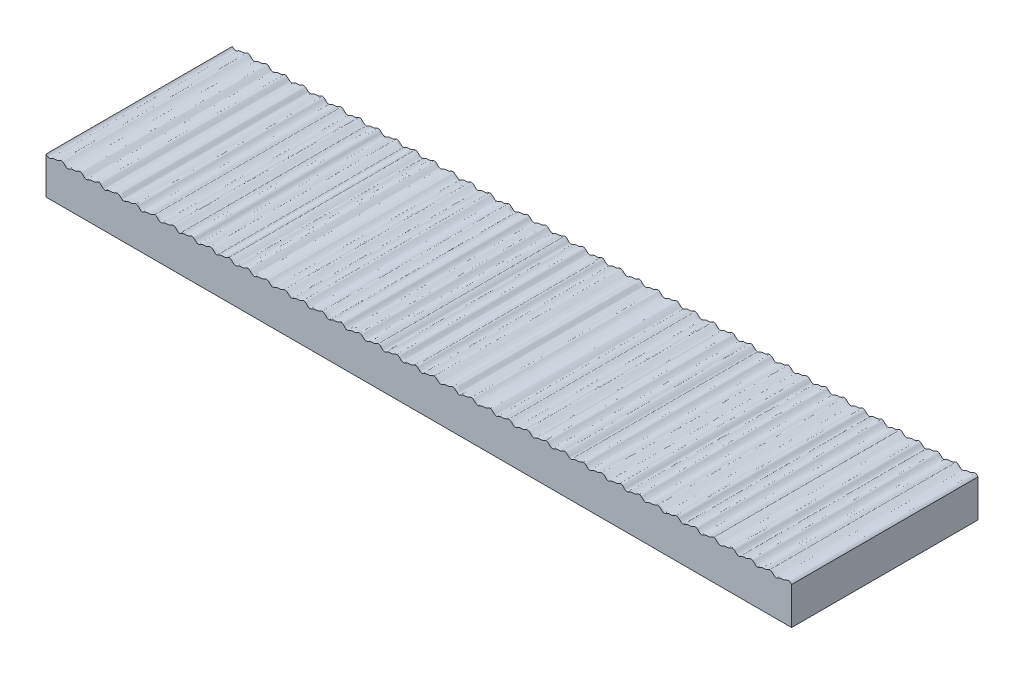
SolidWorks part; units mm, degrees
ref_plane "Ebene vorne" through (0, 0, 0) normal (0, 0, 1) x (1, 0, 0)
ref_plane "Ebene oben" through (0, 0, 0) normal (0, 1, 0) x (1, 0, 0)
ref_plane "Ebene rechts" through (0, 0, 0) normal (1, 0, 0) x (0, 0, -1)
sketch "Skizze1" plane through (0, 0, 0) normal (0, 0, 1) x (1, 0, 0)
  line L0 (0, 10) -> (200, 10) construction
  line L1 (0, 10) -> (0, 0)
  line L2 (0, 0) -> (200, 0)
  line L3 (200, 0) -> (200, 10)
  line L4 (0, 9.5017) -> (200, 9.5017) construction
  line L5 (4.9999, 10) -> (4.9999, 0) construction
  spline S0 degree 4 poles (-19.8, 9.8128) (-19.7132, 9.727) (-19.5652, 9.6108) (-19.3313, 9.4839) (-19.0053, 9.5005) (-18.756, 9.6033) (-18.5037, 9.7471) (-18.2268, 9.8968) (-17.899, 9.9991) (-17.5329, 10.0025) (-17.1781, 9.9937) (-16.8421, 10.0743) (-16.5441, 10.2237) (-16.269, 10.3856) (-15.9702, 10.5157) (-15.6449, 10.5039) (-15.3665, 10.3418) (-15.1366, 10.1344) (-14.8874, 9.8911) (-14.613, 9.6251) (-14.2253, 9.4318) (-13.8044, 9.5667) (-13.4774, 9.7665) (-13.1471, 9.9336) (-12.7787, 10.0119) (-12.3948, 9.9918) (-12.003, 10.014) (-11.6283, 10.1713) (-11.2949, 10.3742) (-10.9166, 10.5481) (-10.5226, 10.4647) (-10.2351, 10.2274) (-9.9864, 9.9872) (-9.7489, 9.7562) (-9.4941, 9.5595) (-9.1984, 9.4737) (-8.9158, 9.5299) (-8.6755, 9.6479) (-8.4177, 9.7964) (-8.1186, 9.9433) (-7.7567, 10.0153) (-7.3586, 9.9875) (-6.9251, 10.0301) (-6.5623, 10.2086) (-6.2539, 10.4005) (-5.9205, 10.5185) (-5.6177, 10.4936) (-5.3452, 10.326) (-5.1071, 10.1058) (-4.8595, 9.8627) (-4.5902, 9.6128) (-4.2208, 9.4424) (-3.8205, 9.5583) (-3.4963, 9.7556) (-3.1609, 9.929) (-2.7804, 10.0137) (-2.3814, 9.9896) (-1.9713, 10.0188) (-1.5811, 10.1958) (-1.257, 10.4006) (-0.9071, 10.5319) (-0.5771, 10.4741) (-0.3263, 10.3084) (-0.0768, 10.0763) (0.056, 9.9441) (0.2767, 9.7371) (0.4956, 9.5743) (0.7544, 9.48) (1.05, 9.5113) (1.3273, 9.6477) (1.6012, 9.8088) (1.9021, 9.9471) (2.2375, 10.009) (2.5868, 9.994) (2.9465, 10.0097) (3.2633, 10.1208) (3.531, 10.269) (3.7764, 10.4067) (4.0174, 10.5009) (4.2937, 10.5121) (4.5645, 10.3933) (4.8005, 10.1959) (5.0283, 9.9711) (5.2688, 9.7419) (5.5521, 9.5241) (5.9206, 9.4608) (6.2669, 9.6123) (6.5703, 9.7924) (6.8913, 9.9463) (7.2504, 10.0115) (7.6239, 9.991) (8.0086, 10.018) (8.3767, 10.1744) (8.6908, 10.3651) (9.0184, 10.5173) (9.3632, 10.5017) (9.6434, 10.3346) (9.8801, 10.1192) (10.1091, 9.8914) (10.3449, 9.6751) (10.622, 9.5036) (10.9686, 9.4786) (11.3025, 9.6302) (11.6207, 9.8248) (11.9967, 9.9846) (12.3936, 10.0089) (12.7833, 9.9873) (13.161, 10.0708) (13.4966, 10.2452) (13.8028, 10.4296) (14.1427, 10.5368) (14.4726, 10.4522) (14.7294, 10.2603) (14.9582, 10.0419) (15.1851, 9.8181) (15.4295, 9.6095) (15.7306, 9.4725) (16.0842, 9.5156) (16.41, 9.6969) (16.7477, 9.8935) (17.1559, 10.0141) (17.5531, 9.9934) (17.9271, 10.0064) (18.2618, 10.12) (18.5491, 10.2781) (18.8425, 10.4467) (19.1956, 10.5461) (19.539, 10.4192) (19.8022, 10.1924) (20.0371, 9.9636) (20.2623, 9.7466) (20.5116, 9.558) (20.8082, 9.4716) (21.1028, 9.5343) (21.3593, 9.6673) (21.617, 9.8163) (21.9007, 9.9454) (22.2191, 10.0064) (22.5538, 9.9968) (22.8831, 10.0033) (23.1957, 10.0912) (23.4781, 10.2368) (23.7453, 10.3932) (24.0343, 10.5142) (24.3441, 10.5037) (24.611, 10.3572) (24.8317, 10.1652) (25.0712, 9.9305) (25.3361, 9.6732) (25.687, 9.4499) (26.0987, 9.5211) (26.4123, 9.6997) (26.6971, 9.8597) (27.0176, 9.9809) (27.371, 10.0095) (27.7381, 9.987) (28.1136, 10.0531) (28.4763, 10.228) (28.8222, 10.4523) (29.2422, 10.5605) (29.6076, 10.3674) (29.8689, 10.1296) (30.0989, 9.9014) (30.3447, 9.6748) (30.6533, 9.4801) (31.0349, 9.4907) (31.3718, 9.6755) (31.6945, 9.8617) (32.0528, 9.9935) (32.4275, 10.0052) (32.7994, 9.9904) (33.1624, 10.0725) (33.4892, 10.2413) (33.7899, 10.4213) (34.1235, 10.5353) (34.4555, 10.4619) (34.7162, 10.2721) (34.9451, 10.0549) (35.1703, 9.8324) (35.4119, 9.6227) (35.7099, 9.4756) (36.0694, 9.5082) (36.4027, 9.6921) (36.7453, 9.8933) (37.1618, 10.016) (37.5686, 9.9916) (37.955, 10.01) (38.3008, 10.1379) (38.5986, 10.3073) (38.8972, 10.4735) (39.2404, 10.5347) (39.5538, 10.4026) (39.7994, 10.1958) (40.0243, 9.9758) (40.2479, 9.7603) (40.5015, 9.5621) (40.8224, 9.4624) (41.1625, 9.5539) (41.4684, 9.7328) (41.7894, 9.9084) (42.1555, 10.0071) (42.5227, 9.9977) (42.8799, 10.0002) (43.2154, 10.0978) (43.5138, 10.257) (43.8102, 10.4307) (44.163, 10.5466) (44.5145, 10.4359) (44.7827, 10.2106) (45.0196, 9.9811) (45.2463, 9.7608) (45.4921, 9.5695) (45.7813, 9.4746) (46.0693, 9.5229) (46.3189, 9.6442) (46.5707, 9.7902) (46.8484, 9.927) (47.1677, 10.0039) (47.5116, 9.9992) (47.8484, 9.9984) (48.169, 10.0798) (48.4573, 10.2246) (48.7268, 10.3831) (49.0125, 10.5086) (49.3176, 10.5095) (49.5819, 10.3772) (49.7978, 10.197) (50.0353, 9.9657) (50.2999, 9.707) (50.6415, 9.4588) (51.0649, 9.5058) (51.3834, 9.6827) (51.6631, 9.8419) (51.976, 9.9702) (52.3236, 10.0107) (52.6857, 9.9883) (53.0576, 10.0353) (53.4288, 10.1996) (53.7766, 10.4255) (54.1972, 10.5686) (54.5817, 10.3889) (54.8482, 10.1492) (55.078, 9.922) (55.3219, 9.6944) (55.6232, 9.4909) (56.0024, 9.48) (56.3413, 9.6571) (56.6566, 9.841) (57.0019, 9.9812) (57.3723, 10.009) (57.7455, 9.9879) (58.1184, 10.0542) (58.4601, 10.2234) (58.7656, 10.4087) (59.0994, 10.5327) (59.4345, 10.4719) (59.6985, 10.2877) (59.9288, 10.0711) (60.1551, 9.8468) (60.395, 9.6354) (60.687, 9.4819) (61.0423, 9.499) (61.374, 9.6742) (61.7071, 9.873) (62.1099, 10.0089) (62.5069, 9.9977) (62.8809, 9.9991) (63.2202, 10.1008) (63.5114, 10.2558) (63.8032, 10.426) (64.1495, 10.5453) (64.5013, 10.4441) (64.7713, 10.2213) (65.0069, 9.9933) (65.2327, 9.7751) (65.5033, 9.5547) (65.884, 9.4445) (66.2644, 9.6064) (66.5993, 9.8128) (66.9589, 9.9696) (67.3267, 10.0107) (67.6846, 9.9895) (68.0293, 10.0315) (68.3405, 10.1598) (68.6192, 10.3197) (68.9196, 10.483) (69.2883, 10.5375) (69.636, 10.3531) (69.9168, 10.0783) (70.2112, 9.7989) (70.5572, 9.4869) (71.0322, 9.466) (71.4097, 9.7065) (71.761, 9.8916) (72.1231, 10.0046) (72.4974, 9.9999) (72.8717, 9.9957) (73.2335, 10.1028) (73.5597, 10.2828) (73.8856, 10.4755) (74.2818, 10.5433) (74.6402, 10.3492) (74.9206, 10.0747) (75.2149, 9.7951) (75.5626, 9.484) (76.0379, 9.4683) (76.4142, 9.7094) (76.7662, 9.8939) (77.1285, 10.0053) (77.5027, 9.9995) (77.877, 9.9963) (78.2383, 10.105) (78.564, 10.2854) (78.8905, 10.4779) (79.2872, 10.5422) (79.6441, 10.3457) (79.9244, 10.0709) (80.2185, 9.7918) (80.5681, 9.4804) (81.0528, 9.4717) (81.4399, 9.7258) (81.8166, 9.9208) (82.2185, 10.0176) (82.6095, 9.9889) (82.983, 10.0173) (83.3181, 10.147) (83.611, 10.3148) (83.9215, 10.4861) (84.3006, 10.537) (84.6481, 10.3407) (84.9279, 10.0713) (85.1793, 9.8221) (85.426, 9.6138) (85.6898, 9.4972) (85.9409, 9.4912) (86.2167, 9.5855) (86.4994, 9.7497) (86.8216, 9.9268) (87.2241, 10.0156) (87.6148, 9.9895) (87.9883, 10.0181) (88.3227, 10.1495) (88.6153, 10.3174) (88.9265, 10.4882) (89.306, 10.5358) (89.6521, 10.3372) (89.9317, 10.0677) (90.1831, 9.8183) (90.4306, 9.6106) (90.6953, 9.4959) (90.9465, 9.4923) (91.2217, 9.5882) (91.5041, 9.7525) (91.8268, 9.9289) (92.2295, 10.0158) (92.6201, 9.9892) (92.9935, 10.0194) (93.3273, 10.1519) (93.6197, 10.32) (93.9314, 10.4902) (94.3114, 10.5345) (94.6561, 10.3336) (94.9354, 10.064) (95.187, 9.8146) (95.4352, 9.6074) (95.7009, 9.4947) (95.9521, 9.4934) (96.2266, 9.5908) (96.5088, 9.7554) (96.832, 9.9311) (97.235, 10.0159) (97.6255, 9.9888) (97.9986, 10.0207) (98.3321, 10.1542) (98.6236, 10.3231) (98.9056, 10.474) (99.2035, 10.5241) (99.4679, 10.4432) (99.6773, 10.3016) (99.8669, 10.1308) (100.0515, 9.949) (100.2431, 9.7658) (100.4584, 9.5966) (100.7245, 9.4824) (101.0266, 9.5028) (101.3082, 9.6369) (101.5812, 9.7975) (101.8792, 9.9391) (102.2124, 10.0078) (102.5609, 9.9957) (102.9197, 10.0051) (103.239, 10.1094) (103.5091, 10.2561) (103.7553, 10.3959) (103.9971, 10.496) (104.2846, 10.5168) (104.5754, 10.3903) (104.8277, 10.1705) (105.0802, 9.92) (105.3443, 9.6707) (105.6839, 9.4635) (106.0872, 9.5085) (106.4264, 9.7098) (106.7634, 9.8963) (107.1347, 10.0069) (107.5036, 9.9984) (107.8569, 9.9988) (108.1849, 10.0861) (108.4725, 10.2335) (108.76, 10.4011) (109.0962, 10.54) (109.4592, 10.4711) (109.7431, 10.2478) (109.9854, 10.0146) (110.2184, 9.7885) (110.4952, 9.5571) (110.8906, 9.4405) (111.2824, 9.6165) (111.6276, 9.8298) (112.0062, 9.9843) (112.3877, 10.0085) (112.7533, 9.9888) (113.0968, 10.0528) (113.3973, 10.1911) (113.6655, 10.3463) (113.9602, 10.4965) (114.3164, 10.5274) (114.6237, 10.3528) (114.8676, 10.1305) (115.0879, 9.9127) (115.2996, 9.7167) (115.5651, 9.5259) (115.9297, 9.4576) (116.3055, 9.6298) (116.6653, 9.853) (117.0908, 10.0124) (117.5404, 9.9944) (117.9485, 10.0031) (118.2912, 10.1356) (118.5689, 10.2905) (118.8107, 10.4241) (119.1178, 10.5331) (119.4895, 10.4658) (119.768, 10.2241) (120.0149, 9.9854) (120.2325, 9.7764) (120.4317, 9.6173) (120.7176, 9.4735) (121.1079, 9.5064) (121.4527, 9.7323) (121.8387, 9.9324) (122.2456, 10.0143) (122.6276, 9.9896) (122.9863, 10.0184) (123.3001, 10.1402) (123.5697, 10.2909) (123.8194, 10.4299) (124.0953, 10.5212) (124.3827, 10.4871) (124.6302, 10.3409) (124.8407, 10.156) (125.0716, 9.9299) (125.3295, 9.6814) (125.6694, 9.4565) (126.0839, 9.5126) (126.4045, 9.6952) (126.6992, 9.8617) (127.03, 9.9848) (127.3919, 10.0088) (127.7645, 9.9868) (128.1421, 10.063) (128.4972, 10.2422) (128.8378, 10.4578) (129.2536, 10.5565) (129.6239, 10.3586) (129.8954, 10.1026) (130.1526, 9.8512) (130.4387, 9.5879) (130.858, 9.4277) (131.2756, 9.61) (131.6255, 9.8302) (132.0056, 9.9826) (132.3786, 10.0086) (132.7414, 9.9891) (133.0874, 10.0485) (133.3951, 10.1892) (133.6732, 10.3519) (133.9828, 10.5071) (134.3571, 10.5201) (134.6871, 10.305) (134.9654, 10.0346) (135.2178, 9.7846) (135.4728, 9.5825) (135.7455, 9.4865) (135.9966, 9.5036) (136.2663, 9.6125) (136.5465, 9.7779) (136.8742, 9.9476) (137.2786, 10.0158) (137.6682, 9.9867) (138.0401, 10.0317) (138.3686, 10.1739) (138.6587, 10.3435) (138.9766, 10.5074) (139.3591, 10.5206) (139.691, 10.3013) (139.9692, 10.031) (140.2217, 9.7808) (140.4776, 9.5795) (140.7512, 9.4857) (141.0022, 9.5051) (141.2712, 9.6153) (141.5513, 9.7807) (141.8795, 9.9496) (142.2841, 10.0157) (142.6736, 9.9865) (143.0452, 10.0332) (143.3732, 10.1764) (143.6631, 10.3461) (143.9817, 10.5092) (144.3643, 10.5188) (144.6948, 10.2977) (144.9729, 10.0273) (145.2255, 9.7771) (145.4824, 9.5765) (145.7568, 9.485) (146.0077, 9.5066) (146.2762, 9.618) (146.5561, 9.7835) (146.8849, 9.9515) (147.2896, 10.0156) (147.679, 9.9864) (148.0503, 10.0347) (148.3778, 10.1788) (148.6673, 10.3489) (148.9827, 10.5084) (149.3547, 10.518) (149.6765, 10.3125) (149.9446, 10.0556) (150.1902, 9.8116) (150.4391, 9.6041) (150.7153, 9.4881) (150.9866, 9.4982) (151.2695, 9.6128) (151.5567, 9.7845) (151.8902, 9.9533) (152.295, 10.0154) (152.6843, 9.9862) (153.0555, 10.0362) (153.3823, 10.1813) (153.6717, 10.3515) (153.9878, 10.5101) (154.3599, 10.5162) (154.6804, 10.309) (154.9483, 10.0519) (155.194, 9.8079) (155.4437, 9.6009) (155.7209, 9.487) (155.9921, 9.4997) (156.2745, 9.6156) (156.5615, 9.7873) (156.8956, 9.9552) (157.3005, 10.0153) (157.6897, 9.9861) (158.0606, 10.0378) (158.3868, 10.1838) (158.6761, 10.3541) (158.9929, 10.5117) (159.3651, 10.5144) (159.6842, 10.3055) (159.952, 10.0482) (160.1979, 9.8042) (160.4484, 9.5978) (160.7265, 9.486) (160.9977, 9.5012) (161.2794, 9.6184) (161.5662, 9.7901) (161.901, 9.9571) (162.306, 10.0151) (162.6951, 9.9859) (163.0657, 10.0394) (163.3914, 10.1863) (163.6804, 10.3567) (163.998, 10.5133) (164.3702, 10.5126) (164.6881, 10.3019) (164.9558, 10.0445) (165.2017, 9.8005) (165.453, 9.5946) (165.7321, 9.485) (166.0032, 9.5027) (166.2843, 9.6213) (166.571, 9.7929) (166.9064, 9.9589) (167.3114, 10.0148) (167.7004, 9.9858) (168.0708, 10.041) (168.3959, 10.1888) (168.6848, 10.3593) (169.0032, 10.5149) (169.3753, 10.5107) (169.6919, 10.2984) (169.9595, 10.0409) (170.2056, 9.7967) (170.4577, 9.5915) (170.7377, 9.4841) (171.0088, 9.5043) (171.2932, 9.6258) (171.5862, 9.8021) (171.9356, 9.9711) (172.3588, 10.0139) (172.7563, 9.9844) (173.1239, 10.06) (173.4361, 10.2123) (173.7115, 10.3743) (174.0212, 10.5173) (174.3841, 10.5062) (174.6957, 10.2949) (174.9632, 10.0372) (175.2094, 9.793) (175.4624, 9.5884) (175.7434, 9.4832) (176.0143, 9.5059) (176.2981, 9.6286) (176.591, 9.8049) (176.941, 9.9728) (177.3642, 10.0135) (177.7617, 9.9845) (178.1289, 10.0619) (178.4406, 10.2148) (178.7159, 10.3769) (179.0222, 10.5164) (179.3746, 10.5061) (179.6774, 10.3095) (179.9347, 10.0656) (180.174, 9.8275) (180.4198, 9.6172) (180.7016, 9.487) (180.993, 9.4969) (181.2955, 9.626) (181.6018, 9.8122) (181.9706, 9.9844) (182.4114, 10.0105) (182.8177, 9.9856) (183.1809, 10.0833) (183.4807, 10.2386) (183.743, 10.3904) (184.0404, 10.5183) (184.3833, 10.5017) (184.6813, 10.3061) (184.9385, 10.0619) (185.1778, 9.8238) (185.4243, 9.6139) (185.7072, 9.4858) (185.9985, 9.4984) (186.3003, 9.6289) (186.6066, 9.815) (186.9761, 9.9859) (187.4168, 10.0099) (187.8231, 9.986) (188.1858, 10.0853) (188.4852, 10.2412) (188.7474, 10.3929) (189.0456, 10.5195) (189.3883, 10.4997) (189.6852, 10.3027) (189.9422, 10.0582) (190.1816, 9.8201) (190.4289, 9.6106) (190.7128, 9.4846) (191.0041, 9.5) (191.3052, 9.6318) (191.6114, 9.8177) (191.9816, 9.9874) (192.4222, 10.0092) (192.8285, 9.9864) (193.1907, 10.0874) (193.4896, 10.2438) (193.7519, 10.3954) (194.0508, 10.5207) (194.3934, 10.4977) (194.6891, 10.2992) (194.9459, 10.0545) (195.1854, 9.8164) (195.4335, 9.6074) (195.7184, 9.4835) (196.0097, 9.5016) (196.3101, 9.6347) (196.6162, 9.8205) (196.9872, 9.9888) (197.4276, 10.0086) (197.8339, 9.9869) (198.1953, 10.0897) (198.4955, 10.2454) (198.7505, 10.4022) (199.1, 10.5235) (199.4629, 10.5031) (199.8859, 10.1151) (200.0712, 9.9273) (200.4553, 9.569) (200.8296, 9.4493) (201.2486, 9.5872) (201.5887, 9.8119) (201.9923, 9.9888) (202.4296, 10.0087) (202.8367, 9.987) (203.1973, 10.0904) (203.4955, 10.2472) (203.7576, 10.3985) (204.057, 10.5219) (204.399, 10.4953) (204.6931, 10.2955) (204.9496, 10.0508) (205.189, 9.8129) (205.4375, 9.6046) (205.7231, 9.4827) (206.014, 9.5029) (206.3136, 9.6368) (206.6195, 9.8223) (206.9906, 9.9896) (207.4305, 10.0082) (207.8363, 9.9872) (208.1974, 10.0903) (208.4955, 10.2472) (208.7576, 10.3985) (209.057, 10.5219) (209.399, 10.4953) (209.6931, 10.2955) (209.9496, 10.0508) (210.189, 9.8129) (210.4375, 9.6046) (210.7231, 9.4827) (211.014, 9.5029) (211.3136, 9.6368) (211.6195, 9.8223) (211.9906, 9.9896) (212.4305, 10.0082) (212.8363, 9.9872) (213.1974, 10.0903) (213.4955, 10.2472) (213.7576, 10.3985) (214.057, 10.5219) (214.399, 10.4953) (214.6931, 10.2955) (214.9496, 10.0508) (215.189, 9.8129) (215.4375, 9.6046) (215.7231, 9.4827) (216.014, 9.5029) (216.3123, 9.6363) (216.6162, 9.8202) (216.983, 9.9866) (217.4171, 10.0097) (217.8329, 9.9851) (218.2196, 10.096) (218.5508, 10.2782) (218.8619, 10.4609) (219.2613, 10.5498) (219.5473, 10.4039) (219.7135, 10.273) (219.7999, 10.1873) knots 0 0 0 0 0 0.001825 0.002828 0.003831 0.004834 0.005837 0.007212 0.008586 0.009961 0.011336 0.012548 0.013761 0.014973 0.016185 0.017355 0.018526 0.019697 0.020867 0.022616 0.024365 0.025745 0.027126 0.028507 0.029888 0.031392 0.032896 0.0344 0.035904 0.037402 0.0389 0.040156 0.041413 0.042669 0.043926 0.044928 0.04593 0.046932 0.047934 0.049435 0.050935 0.052436 0.053937 0.055942 0.056945 0.057948 0.059177 0.060406 0.061634 0.062863 0.064424 0.065985 0.067399 0.068812 0.070226 0.07164 0.073225 0.07481 0.076395 0.077981 0.079102 0.080224 0.081345 0.082467 0.083446 0.084425 0.085404 0.086382 0.087588 0.088794 0.09 0.091205 0.092557 0.093908 0.095259 0.096611 0.097574 0.098537 0.0995 0.100463 0.101676 0.102889 0.104101 0.105314 0.106733 0.108153 0.109481 0.11081 0.112139 0.113468 0.114953 0.116437 0.117921 0.119406 0.120574 0.121743 0.122967 0.124191 0.125415 0.126639 0.12781 0.12898 0.130495 0.132009 0.133523 0.135038 0.136457 0.137876 0.139295 0.140715 0.141888 0.14306 0.144268 0.145476 0.146684 0.147892 0.149098 0.150303 0.151879 0.153455 0.155031 0.156607 0.157844 0.159081 0.160318 0.161555 0.162973 0.164392 0.165578 0.166763 0.167949 0.169135 0.170218 0.1713 0.172383 0.173465 0.174725 0.175985 0.177244 0.178504 0.179678 0.180853 0.182027 0.183201 0.184304 0.185406 0.186508 0.187611 0.189357 0.191103 0.192337 0.193571 0.194805 0.196039 0.197468 0.198897 0.200326 0.201755 0.203476 0.205198 0.20642 0.207641 0.208863 0.210085 0.211511 0.212937 0.214355 0.215773 0.217192 0.21861 0.21999 0.22137 0.22275 0.224131 0.22532 0.22651 0.227709 0.228909 0.230108 0.231307 0.232532 0.233758 0.235363 0.236968 0.238574 0.240179 0.241478 0.242776 0.244074 0.245373 0.246608 0.247843 0.24902 0.250198 0.251375 0.252553 0.25382 0.255088 0.256503 0.257917 0.259332 0.260747 0.262019 0.263291 0.264562 0.265834 0.267249 0.268663 0.269862 0.27106 0.272259 0.273457 0.274494 0.275531 0.276569 0.277606 0.278899 0.280193 0.281486 0.282779 0.283965 0.285151 0.286337 0.287523 0.28858 0.289637 0.290694 0.291751 0.293566 0.295382 0.2966 0.297819 0.299037 0.300256 0.301665 0.303074 0.304484 0.305893 0.307685 0.309477 0.310696 0.311916 0.313135 0.314354 0.315781 0.317208 0.318594 0.319979 0.321364 0.32275 0.324175 0.325601 0.327026 0.328452 0.329623 0.330795 0.332002 0.333209 0.334416 0.335623 0.336827 0.338031 0.339603 0.341175 0.342747 0.344319 0.34556 0.346802 0.348044 0.349286 0.350701 0.352117 0.353306 0.354496 0.355685 0.356875 0.358525 0.360175 0.361565 0.362955 0.364345 0.365735 0.366952 0.368169 0.369386 0.370604 0.372081 0.373559 0.375036 0.376514 0.378379 0.380245 0.381651 0.383058 0.384465 0.385872 0.387278 0.388685 0.390092 0.391499 0.392976 0.394454 0.395932 0.39741 0.399276 0.401142 0.402548 0.403955 0.405361 0.406768 0.408174 0.409581 0.410987 0.412393 0.413872 0.41535 0.416829 0.418307 0.420173 0.422039 0.423572 0.425106 0.42664 0.428174 0.429453 0.430732 0.432011 0.43329 0.434768 0.436247 0.437726 0.439204 0.440138 0.441071 0.442004 0.442937 0.44447 0.446004 0.447537 0.449071 0.450349 0.451628 0.452907 0.454186 0.455665 0.457144 0.458623 0.460102 0.461035 0.461969 0.462902 0.463835 0.465368 0.466901 0.468435 0.469968 0.471246 0.472525 0.473803 0.475082 0.476561 0.478041 0.47952 0.481 0.481933 0.482867 0.4838 0.484733 0.486266 0.487799 0.489332 0.490865 0.492143 0.493421 0.494699 0.495978 0.496919 0.49786 0.498801 0.499743 0.500767 0.501791 0.502815 0.503839 0.505041 0.506243 0.507445 0.508647 0.509994 0.511342 0.51269 0.514038 0.515013 0.515988 0.516963 0.517937 0.519284 0.52063 0.521976 0.523322 0.52483 0.526337 0.527779 0.529221 0.530664 0.532106 0.53332 0.534535 0.535749 0.536964 0.538398 0.539832 0.541062 0.542291 0.543521 0.54475 0.54646 0.548169 0.54961 0.55105 0.55249 0.553931 0.555106 0.556282 0.557457 0.558632 0.560047 0.561462 0.562554 0.563646 0.564737 0.565829 0.567413 0.568996 0.570687 0.572377 0.574067 0.575758 0.576801 0.577844 0.578887 0.57993 0.581611 0.583292 0.58425 0.585207 0.586164 0.587121 0.588974 0.590827 0.592267 0.593707 0.595146 0.596586 0.597664 0.598742 0.59982 0.600898 0.601955 0.603011 0.604068 0.605124 0.606828 0.608532 0.609812 0.611093 0.612373 0.613653 0.615095 0.616536 0.617978 0.619419 0.621046 0.622673 0.62403 0.625387 0.626744 0.628101 0.62991 0.631718 0.633128 0.634538 0.635947 0.637357 0.638579 0.639802 0.641024 0.642246 0.643729 0.645212 0.646695 0.648178 0.649113 0.650047 0.650982 0.651917 0.653447 0.654977 0.656507 0.658037 0.659313 0.66059 0.661866 0.663142 0.664625 0.666109 0.667592 0.669076 0.670011 0.670945 0.67188 0.672815 0.674345 0.675875 0.677404 0.678934 0.68021 0.681486 0.682762 0.684038 0.685522 0.687006 0.68849 0.689973 0.690908 0.691843 0.692778 0.693713 0.695243 0.696772 0.698302 0.699831 0.701107 0.702382 0.703658 0.704934 0.706349 0.707764 0.709179 0.710594 0.711598 0.712602 0.713607 0.714611 0.71614 0.717669 0.719198 0.720727 0.722003 0.723278 0.724553 0.725829 0.727244 0.72866 0.730075 0.731491 0.732495 0.7335 0.734504 0.735509 0.737037 0.738566 0.740095 0.741624 0.742899 0.744174 0.745449 0.746724 0.74814 0.749556 0.750972 0.752387 0.753392 0.754397 0.755402 0.756406 0.757935 0.759463 0.760991 0.76252 0.763795 0.765069 0.766344 0.767619 0.769035 0.770452 0.771868 0.773284 0.774289 0.775294 0.776299 0.777304 0.778832 0.78036 0.781888 0.783416 0.78469 0.785965 0.78724 0.788514 0.789931 0.791348 0.792764 0.794181 0.795186 0.796191 0.797196 0.798202 0.799792 0.801383 0.802973 0.804564 0.805775 0.806987 0.808198 0.80941 0.810827 0.812244 0.813661 0.815078 0.816084 0.817089 0.818095 0.8191 0.82069 0.82228 0.82387 0.82546 0.826672 0.827883 0.829094 0.830306 0.831654 0.833002 0.83435 0.835698 0.836773 0.837848 0.838923 0.839998 0.84165 0.843303 0.844955 0.846608 0.847756 0.848905 0.850053 0.851201 0.85255 0.853899 0.855247 0.856596 0.857671 0.858746 0.859821 0.860896 0.862548 0.8642 0.865852 0.867505 0.868653 0.869801 0.870949 0.872097 0.873446 0.874795 0.876144 0.877493 0.878568 0.879644 0.880719 0.881794 0.883446 0.885098 0.88675 0.888401 0.889549 0.890697 0.891845 0.892993 0.894342 0.895692 0.897041 0.89839 0.899466 0.900542 0.901617 0.902693 0.904344 0.905996 0.907647 0.909298 0.910446 0.911594 0.912741 0.913889 0.915711 0.917533 0.919046 0.920559 0.922072 0.923585 0.925235 0.926884 0.928534 0.930183 0.93133 0.932476 0.933623 0.934769 0.936118 0.937466 0.938814 0.940163 0.941238 0.942313 0.943388 0.944462 0.946112 0.947761 0.949411 0.95106 0.952207 0.953353 0.9545 0.955646 0.956994 0.958343 0.959691 0.96104 0.962115 0.96319 0.964265 0.965339 0.966989 0.968638 0.970288 0.971937 0.973084 0.97423 0.975377 0.976523 0.977871 0.97922 0.980568 0.981917 0.982992 0.984067 0.985141 0.986216 0.987846 0.989475 0.991104 0.992733 0.994094 0.995454 0.996814 0.998175 1 1 1 1 1 construction
  spline S1 degree 4 poles (0, 10) (0.0389, 9.9624) (0.117, 9.8869) (0.2767, 9.7371) (0.4956, 9.5743) (0.7544, 9.48) (1.05, 9.5113) (1.3273, 9.6477) (1.6012, 9.8088) (1.9021, 9.9471) (2.2375, 10.009) (2.5868, 9.994) (2.9465, 10.0097) (3.2633, 10.1208) (3.531, 10.269) (3.7764, 10.4067) (4.0174, 10.5009) (4.2937, 10.5121) (4.5645, 10.3933) (4.8005, 10.1959) (5.0283, 9.9711) (5.2688, 9.7419) (5.5521, 9.5241) (5.9206, 9.4608) (6.2669, 9.6123) (6.5703, 9.7924) (6.8913, 9.9463) (7.2504, 10.0115) (7.6239, 9.991) (8.0086, 10.018) (8.3767, 10.1744) (8.6908, 10.3651) (9.0184, 10.5173) (9.3632, 10.5017) (9.6434, 10.3346) (9.8801, 10.1192) (10.1091, 9.8914) (10.3449, 9.6751) (10.622, 9.5036) (10.9686, 9.4786) (11.3025, 9.6302) (11.6207, 9.8248) (11.9967, 9.9846) (12.3936, 10.0089) (12.7833, 9.9873) (13.161, 10.0708) (13.4966, 10.2452) (13.8028, 10.4296) (14.1427, 10.5368) (14.4726, 10.4522) (14.7294, 10.2603) (14.9582, 10.0419) (15.1851, 9.8181) (15.4295, 9.6095) (15.7306, 9.4725) (16.0842, 9.5156) (16.41, 9.6969) (16.7477, 9.8935) (17.1559, 10.0141) (17.5531, 9.9934) (17.9271, 10.0064) (18.2618, 10.12) (18.5491, 10.2781) (18.8425, 10.4467) (19.1956, 10.5461) (19.539, 10.4192) (19.8022, 10.1924) (20.0371, 9.9636) (20.2623, 9.7466) (20.5116, 9.558) (20.8082, 9.4716) (21.1028, 9.5343) (21.3593, 9.6673) (21.617, 9.8163) (21.9007, 9.9454) (22.2191, 10.0064) (22.5538, 9.9968) (22.8831, 10.0033) (23.1957, 10.0912) (23.4781, 10.2368) (23.7453, 10.3932) (24.0343, 10.5142) (24.3441, 10.5037) (24.611, 10.3572) (24.8317, 10.1652) (25.0712, 9.9305) (25.3361, 9.6732) (25.687, 9.4499) (26.0987, 9.5211) (26.4123, 9.6997) (26.6971, 9.8597) (27.0176, 9.9809) (27.371, 10.0095) (27.7381, 9.987) (28.1136, 10.0531) (28.4763, 10.228) (28.8222, 10.4523) (29.2422, 10.5605) (29.6076, 10.3674) (29.8689, 10.1296) (30.0989, 9.9014) (30.3447, 9.6748) (30.6533, 9.4801) (31.0349, 9.4907) (31.3718, 9.6755) (31.6945, 9.8617) (32.0528, 9.9935) (32.4275, 10.0052) (32.7994, 9.9904) (33.1624, 10.0725) (33.4892, 10.2413) (33.7899, 10.4213) (34.1235, 10.5353) (34.4555, 10.4619) (34.7162, 10.2721) (34.9451, 10.0549) (35.1703, 9.8324) (35.4119, 9.6227) (35.7099, 9.4756) (36.0694, 9.5082) (36.4027, 9.6921) (36.7453, 9.8933) (37.1618, 10.016) (37.5686, 9.9916) (37.955, 10.01) (38.3008, 10.1379) (38.5986, 10.3073) (38.8972, 10.4735) (39.2404, 10.5347) (39.5538, 10.4026) (39.7994, 10.1958) (40.0243, 9.9758) (40.2479, 9.7603) (40.5015, 9.5621) (40.8224, 9.4624) (41.1625, 9.5539) (41.4684, 9.7328) (41.7894, 9.9084) (42.1555, 10.0071) (42.5227, 9.9977) (42.8799, 10.0002) (43.2154, 10.0978) (43.5138, 10.257) (43.8102, 10.4307) (44.163, 10.5466) (44.5145, 10.4359) (44.7827, 10.2106) (45.0196, 9.9811) (45.2463, 9.7608) (45.4921, 9.5695) (45.7813, 9.4746) (46.0693, 9.5229) (46.3189, 9.6442) (46.5707, 9.7902) (46.8484, 9.927) (47.1677, 10.0039) (47.5116, 9.9992) (47.8484, 9.9984) (48.169, 10.0798) (48.4573, 10.2246) (48.7268, 10.3831) (49.0125, 10.5086) (49.3176, 10.5095) (49.5819, 10.3772) (49.7978, 10.197) (50.0353, 9.9657) (50.2999, 9.707) (50.6415, 9.4588) (51.0649, 9.5058) (51.3834, 9.6827) (51.6631, 9.8419) (51.976, 9.9702) (52.3236, 10.0107) (52.6857, 9.9883) (53.0576, 10.0353) (53.4288, 10.1996) (53.7766, 10.4255) (54.1972, 10.5686) (54.5817, 10.3889) (54.8482, 10.1492) (55.078, 9.922) (55.3219, 9.6944) (55.6232, 9.4909) (56.0024, 9.48) (56.3413, 9.6571) (56.6566, 9.841) (57.0019, 9.9812) (57.3723, 10.009) (57.7455, 9.9879) (58.1184, 10.0542) (58.4601, 10.2234) (58.7656, 10.4087) (59.0994, 10.5327) (59.4345, 10.4719) (59.6985, 10.2877) (59.9288, 10.0711) (60.1551, 9.8468) (60.395, 9.6354) (60.687, 9.4819) (61.0423, 9.499) (61.374, 9.6742) (61.7071, 9.873) (62.1099, 10.0089) (62.5069, 9.9977) (62.8809, 9.9991) (63.2202, 10.1008) (63.5114, 10.2558) (63.8032, 10.426) (64.1495, 10.5453) (64.5013, 10.4441) (64.7713, 10.2213) (65.0069, 9.9933) (65.2327, 9.7751) (65.5033, 9.5547) (65.884, 9.4445) (66.2644, 9.6064) (66.5993, 9.8128) (66.9589, 9.9696) (67.3267, 10.0107) (67.6846, 9.9895) (68.0293, 10.0315) (68.3405, 10.1598) (68.6192, 10.3197) (68.9196, 10.483) (69.2883, 10.5375) (69.636, 10.3531) (69.9168, 10.0783) (70.2112, 9.7989) (70.5572, 9.4869) (71.0322, 9.466) (71.4097, 9.7065) (71.761, 9.8916) (72.1231, 10.0046) (72.4974, 9.9999) (72.8717, 9.9957) (73.2335, 10.1028) (73.5597, 10.2828) (73.8856, 10.4755) (74.2818, 10.5433) (74.6402, 10.3492) (74.9206, 10.0747) (75.2149, 9.7951) (75.5626, 9.484) (76.0379, 9.4683) (76.4142, 9.7094) (76.7662, 9.8939) (77.1285, 10.0053) (77.5027, 9.9995) (77.877, 9.9963) (78.2383, 10.105) (78.564, 10.2854) (78.8905, 10.4779) (79.2872, 10.5422) (79.6441, 10.3457) (79.9244, 10.0709) (80.2185, 9.7918) (80.5681, 9.4804) (81.0528, 9.4717) (81.4399, 9.7258) (81.8166, 9.9208) (82.2185, 10.0176) (82.6095, 9.9889) (82.983, 10.0173) (83.3181, 10.147) (83.611, 10.3148) (83.9215, 10.4861) (84.3006, 10.537) (84.6481, 10.3407) (84.9279, 10.0713) (85.1793, 9.8221) (85.426, 9.6138) (85.6898, 9.4972) (85.9409, 9.4912) (86.2167, 9.5855) (86.4994, 9.7497) (86.8216, 9.9268) (87.2241, 10.0156) (87.6148, 9.9895) (87.9883, 10.0181) (88.3227, 10.1495) (88.6153, 10.3174) (88.9265, 10.4882) (89.306, 10.5358) (89.6521, 10.3372) (89.9317, 10.0677) (90.1831, 9.8183) (90.4306, 9.6106) (90.6953, 9.4959) (90.9465, 9.4923) (91.2217, 9.5882) (91.5041, 9.7525) (91.8268, 9.9289) (92.2295, 10.0158) (92.6201, 9.9892) (92.9935, 10.0194) (93.3273, 10.1519) (93.6197, 10.32) (93.9314, 10.4902) (94.3114, 10.5345) (94.6561, 10.3336) (94.9354, 10.064) (95.187, 9.8146) (95.4352, 9.6074) (95.7009, 9.4947) (95.9521, 9.4934) (96.2266, 9.5908) (96.5088, 9.7554) (96.832, 9.9311) (97.235, 10.0159) (97.6255, 9.9888) (97.9986, 10.0207) (98.3321, 10.1542) (98.6236, 10.3231) (98.9056, 10.474) (99.2035, 10.5241) (99.4679, 10.4432) (99.6773, 10.3016) (99.8669, 10.1308) (100.0515, 9.949) (100.2431, 9.7658) (100.4584, 9.5966) (100.7245, 9.4824) (101.0266, 9.5028) (101.3082, 9.6369) (101.5812, 9.7975) (101.8792, 9.9391) (102.2124, 10.0078) (102.5609, 9.9957) (102.9197, 10.0051) (103.239, 10.1094) (103.5091, 10.2561) (103.7553, 10.3959) (103.9971, 10.496) (104.2846, 10.5168) (104.5754, 10.3903) (104.8277, 10.1705) (105.0802, 9.92) (105.3443, 9.6707) (105.6839, 9.4635) (106.0872, 9.5085) (106.4264, 9.7098) (106.7634, 9.8963) (107.1347, 10.0069) (107.5036, 9.9984) (107.8569, 9.9988) (108.1849, 10.0861) (108.4725, 10.2335) (108.76, 10.4011) (109.0962, 10.54) (109.4592, 10.4711) (109.7431, 10.2478) (109.9854, 10.0146) (110.2184, 9.7885) (110.4952, 9.5571) (110.8906, 9.4405) (111.2824, 9.6165) (111.6276, 9.8298) (112.0062, 9.9843) (112.3877, 10.0085) (112.7533, 9.9888) (113.0968, 10.0528) (113.3973, 10.1911) (113.6655, 10.3463) (113.9602, 10.4965) (114.3164, 10.5274) (114.6237, 10.3528) (114.8676, 10.1305) (115.0879, 9.9127) (115.2996, 9.7167) (115.5651, 9.5259) (115.9297, 9.4576) (116.3055, 9.6298) (116.6653, 9.853) (117.0908, 10.0124) (117.5404, 9.9944) (117.9485, 10.0031) (118.2912, 10.1356) (118.5689, 10.2905) (118.8107, 10.4241) (119.1178, 10.5331) (119.4895, 10.4658) (119.768, 10.2241) (120.0149, 9.9854) (120.2325, 9.7764) (120.4317, 9.6173) (120.7176, 9.4735) (121.1079, 9.5064) (121.4527, 9.7323) (121.8387, 9.9324) (122.2456, 10.0143) (122.6276, 9.9896) (122.9863, 10.0184) (123.3001, 10.1402) (123.5697, 10.2909) (123.8194, 10.4299) (124.0953, 10.5212) (124.3827, 10.4871) (124.6302, 10.3409) (124.8407, 10.156) (125.0716, 9.9299) (125.3295, 9.6814) (125.6694, 9.4565) (126.0839, 9.5126) (126.4045, 9.6952) (126.6992, 9.8617) (127.03, 9.9848) (127.3919, 10.0088) (127.7645, 9.9868) (128.1421, 10.063) (128.4972, 10.2422) (128.8378, 10.4578) (129.2536, 10.5565) (129.6239, 10.3586) (129.8954, 10.1026) (130.1526, 9.8512) (130.4387, 9.5879) (130.858, 9.4277) (131.2756, 9.61) (131.6255, 9.8302) (132.0056, 9.9826) (132.3786, 10.0086) (132.7414, 9.9891) (133.0874, 10.0485) (133.3951, 10.1892) (133.6732, 10.3519) (133.9828, 10.5071) (134.3571, 10.5201) (134.6871, 10.305) (134.9654, 10.0346) (135.2178, 9.7846) (135.4728, 9.5825) (135.7455, 9.4865) (135.9966, 9.5036) (136.2663, 9.6125) (136.5465, 9.7779) (136.8742, 9.9476) (137.2786, 10.0158) (137.6682, 9.9867) (138.0401, 10.0317) (138.3686, 10.1739) (138.6587, 10.3435) (138.9766, 10.5074) (139.3591, 10.5206) (139.691, 10.3013) (139.9692, 10.031) (140.2217, 9.7808) (140.4776, 9.5795) (140.7512, 9.4857) (141.0022, 9.5051) (141.2712, 9.6153) (141.5513, 9.7807) (141.8795, 9.9496) (142.2841, 10.0157) (142.6736, 9.9865) (143.0452, 10.0332) (143.3732, 10.1764) (143.6631, 10.3461) (143.9817, 10.5092) (144.3643, 10.5188) (144.6948, 10.2977) (144.9729, 10.0273) (145.2255, 9.7771) (145.4824, 9.5765) (145.7568, 9.485) (146.0077, 9.5066) (146.2762, 9.618) (146.5561, 9.7835) (146.8849, 9.9515) (147.2896, 10.0156) (147.679, 9.9864) (148.0503, 10.0347) (148.3778, 10.1788) (148.6673, 10.3489) (148.9827, 10.5084) (149.3547, 10.518) (149.6765, 10.3125) (149.9446, 10.0556) (150.1902, 9.8116) (150.4391, 9.6041) (150.7153, 9.4881) (150.9866, 9.4982) (151.2695, 9.6128) (151.5567, 9.7845) (151.8902, 9.9533) (152.295, 10.0154) (152.6843, 9.9862) (153.0555, 10.0362) (153.3823, 10.1813) (153.6717, 10.3515) (153.9878, 10.5101) (154.3599, 10.5162) (154.6804, 10.309) (154.9483, 10.0519) (155.194, 9.8079) (155.4437, 9.6009) (155.7209, 9.487) (155.9921, 9.4997) (156.2745, 9.6156) (156.5615, 9.7873) (156.8956, 9.9552) (157.3005, 10.0153) (157.6897, 9.9861) (158.0606, 10.0378) (158.3868, 10.1838) (158.6761, 10.3541) (158.9929, 10.5117) (159.3651, 10.5144) (159.6842, 10.3055) (159.952, 10.0482) (160.1979, 9.8042) (160.4484, 9.5978) (160.7265, 9.486) (160.9977, 9.5012) (161.2794, 9.6184) (161.5662, 9.7901) (161.901, 9.9571) (162.306, 10.0151) (162.6951, 9.9859) (163.0657, 10.0394) (163.3914, 10.1863) (163.6804, 10.3567) (163.998, 10.5133) (164.3702, 10.5126) (164.6881, 10.3019) (164.9558, 10.0445) (165.2017, 9.8005) (165.453, 9.5946) (165.7321, 9.485) (166.0032, 9.5027) (166.2843, 9.6213) (166.571, 9.7929) (166.9064, 9.9589) (167.3114, 10.0148) (167.7004, 9.9858) (168.0708, 10.041) (168.3959, 10.1888) (168.6848, 10.3593) (169.0032, 10.5149) (169.3753, 10.5107) (169.6919, 10.2984) (169.9595, 10.0409) (170.2056, 9.7967) (170.4577, 9.5915) (170.7377, 9.4841) (171.0088, 9.5043) (171.2932, 9.6258) (171.5862, 9.8021) (171.9356, 9.9711) (172.3588, 10.0139) (172.7563, 9.9844) (173.1239, 10.06) (173.4361, 10.2123) (173.7115, 10.3743) (174.0212, 10.5173) (174.3841, 10.5062) (174.6957, 10.2949) (174.9632, 10.0372) (175.2094, 9.793) (175.4624, 9.5884) (175.7434, 9.4832) (176.0143, 9.5059) (176.2981, 9.6286) (176.591, 9.8049) (176.941, 9.9728) (177.3642, 10.0135) (177.7617, 9.9845) (178.1289, 10.0619) (178.4406, 10.2148) (178.7159, 10.3769) (179.0222, 10.5164) (179.3746, 10.5061) (179.6774, 10.3095) (179.9347, 10.0656) (180.174, 9.8275) (180.4198, 9.6172) (180.7016, 9.487) (180.993, 9.4969) (181.2955, 9.626) (181.6018, 9.8122) (181.9706, 9.9844) (182.4114, 10.0105) (182.8177, 9.9856) (183.1809, 10.0833) (183.4807, 10.2386) (183.743, 10.3904) (184.0404, 10.5183) (184.3833, 10.5017) (184.6813, 10.3061) (184.9385, 10.0619) (185.1778, 9.8238) (185.4243, 9.6139) (185.7072, 9.4858) (185.9985, 9.4984) (186.3003, 9.6289) (186.6066, 9.815) (186.9761, 9.9859) (187.4168, 10.0099) (187.8231, 9.986) (188.1858, 10.0853) (188.4852, 10.2412) (188.7474, 10.3929) (189.0456, 10.5195) (189.3883, 10.4997) (189.6852, 10.3027) (189.9422, 10.0582) (190.1816, 9.8201) (190.4289, 9.6106) (190.7128, 9.4846) (191.0041, 9.5) (191.3052, 9.6318) (191.6114, 9.8177) (191.9816, 9.9874) (192.4222, 10.0092) (192.8285, 9.9864) (193.1907, 10.0874) (193.4896, 10.2438) (193.7519, 10.3954) (194.0508, 10.5207) (194.3934, 10.4977) (194.6891, 10.2992) (194.9459, 10.0545) (195.1854, 9.8164) (195.4335, 9.6074) (195.7184, 9.4835) (196.0097, 9.5016) (196.3101, 9.6347) (196.6162, 9.8205) (196.9872, 9.9888) (197.4276, 10.0086) (197.8339, 9.9869) (198.1953, 10.0897) (198.4955, 10.2454) (198.7505, 10.4022) (199.1, 10.5235) (199.4629, 10.5031) (199.7844, 10.2082) (199.9276, 10.0699) (200, 10) knots 0.082467 0.082467 0.082467 0.082467 0.082467 0.083446 0.084425 0.085404 0.086382 0.087588 0.088794 0.09 0.091205 0.092557 0.093908 0.095259 0.096611 0.097574 0.098537 0.0995 0.100463 0.101676 0.102889 0.104101 0.105314 0.106733 0.108153 0.109481 0.11081 0.112139 0.113468 0.114953 0.116437 0.117921 0.119406 0.120574 0.121743 0.122967 0.124191 0.125415 0.126639 0.12781 0.12898 0.130495 0.132009 0.133523 0.135038 0.136457 0.137876 0.139295 0.140715 0.141888 0.14306 0.144268 0.145476 0.146684 0.147892 0.149098 0.150303 0.151879 0.153455 0.155031 0.156607 0.157844 0.159081 0.160318 0.161555 0.162973 0.164392 0.165578 0.166763 0.167949 0.169135 0.170218 0.1713 0.172383 0.173465 0.174725 0.175985 0.177244 0.178504 0.179678 0.180853 0.182027 0.183201 0.184304 0.185406 0.186508 0.187611 0.189357 0.191103 0.192337 0.193571 0.194805 0.196039 0.197468 0.198897 0.200326 0.201755 0.203476 0.205198 0.20642 0.207641 0.208863 0.210085 0.211511 0.212937 0.214355 0.215773 0.217192 0.21861 0.21999 0.22137 0.22275 0.224131 0.22532 0.22651 0.227709 0.228909 0.230108 0.231307 0.232532 0.233758 0.235363 0.236968 0.238574 0.240179 0.241478 0.242776 0.244074 0.245373 0.246608 0.247843 0.24902 0.250198 0.251375 0.252553 0.25382 0.255088 0.256503 0.257917 0.259332 0.260747 0.262019 0.263291 0.264562 0.265834 0.267249 0.268663 0.269862 0.27106 0.272259 0.273457 0.274494 0.275531 0.276569 0.277606 0.278899 0.280193 0.281486 0.282779 0.283965 0.285151 0.286337 0.287523 0.28858 0.289637 0.290694 0.291751 0.293566 0.295382 0.2966 0.297819 0.299037 0.300256 0.301665 0.303074 0.304484 0.305893 0.307685 0.309477 0.310696 0.311916 0.313135 0.314354 0.315781 0.317208 0.318594 0.319979 0.321364 0.32275 0.324175 0.325601 0.327026 0.328452 0.329623 0.330795 0.332002 0.333209 0.334416 0.335623 0.336827 0.338031 0.339603 0.341175 0.342747 0.344319 0.34556 0.346802 0.348044 0.349286 0.350701 0.352117 0.353306 0.354496 0.355685 0.356875 0.358525 0.360175 0.361565 0.362955 0.364345 0.365735 0.366952 0.368169 0.369386 0.370604 0.372081 0.373559 0.375036 0.376514 0.378379 0.380245 0.381651 0.383058 0.384465 0.385872 0.387278 0.388685 0.390092 0.391499 0.392976 0.394454 0.395932 0.39741 0.399276 0.401142 0.402548 0.403955 0.405361 0.406768 0.408174 0.409581 0.410987 0.412393 0.413872 0.41535 0.416829 0.418307 0.420173 0.422039 0.423572 0.425106 0.42664 0.428174 0.429453 0.430732 0.432011 0.43329 0.434768 0.436247 0.437726 0.439204 0.440138 0.441071 0.442004 0.442937 0.44447 0.446004 0.447537 0.449071 0.450349 0.451628 0.452907 0.454186 0.455665 0.457144 0.458623 0.460102 0.461035 0.461969 0.462902 0.463835 0.465368 0.466901 0.468435 0.469968 0.471246 0.472525 0.473803 0.475082 0.476561 0.478041 0.47952 0.481 0.481933 0.482867 0.4838 0.484733 0.486266 0.487799 0.489332 0.490865 0.492143 0.493421 0.494699 0.495978 0.496919 0.49786 0.498801 0.499743 0.500767 0.501791 0.502815 0.503839 0.505041 0.506243 0.507445 0.508647 0.509994 0.511342 0.51269 0.514038 0.515013 0.515988 0.516963 0.517937 0.519284 0.52063 0.521976 0.523322 0.52483 0.526337 0.527779 0.529221 0.530664 0.532106 0.53332 0.534535 0.535749 0.536964 0.538398 0.539832 0.541062 0.542291 0.543521 0.54475 0.54646 0.548169 0.54961 0.55105 0.55249 0.553931 0.555106 0.556282 0.557457 0.558632 0.560047 0.561462 0.562554 0.563646 0.564737 0.565829 0.567413 0.568996 0.570687 0.572377 0.574067 0.575758 0.576801 0.577844 0.578887 0.57993 0.581611 0.583292 0.58425 0.585207 0.586164 0.587121 0.588974 0.590827 0.592267 0.593707 0.595146 0.596586 0.597664 0.598742 0.59982 0.600898 0.601955 0.603011 0.604068 0.605124 0.606828 0.608532 0.609812 0.611093 0.612373 0.613653 0.615095 0.616536 0.617978 0.619419 0.621046 0.622673 0.62403 0.625387 0.626744 0.628101 0.62991 0.631718 0.633128 0.634538 0.635947 0.637357 0.638579 0.639802 0.641024 0.642246 0.643729 0.645212 0.646695 0.648178 0.649113 0.650047 0.650982 0.651917 0.653447 0.654977 0.656507 0.658037 0.659313 0.66059 0.661866 0.663142 0.664625 0.666109 0.667592 0.669076 0.670011 0.670945 0.67188 0.672815 0.674345 0.675875 0.677404 0.678934 0.68021 0.681486 0.682762 0.684038 0.685522 0.687006 0.68849 0.689973 0.690908 0.691843 0.692778 0.693713 0.695243 0.696772 0.698302 0.699831 0.701107 0.702382 0.703658 0.704934 0.706349 0.707764 0.709179 0.710594 0.711598 0.712602 0.713607 0.714611 0.71614 0.717669 0.719198 0.720727 0.722003 0.723278 0.724553 0.725829 0.727244 0.72866 0.730075 0.731491 0.732495 0.7335 0.734504 0.735509 0.737037 0.738566 0.740095 0.741624 0.742899 0.744174 0.745449 0.746724 0.74814 0.749556 0.750972 0.752387 0.753392 0.754397 0.755402 0.756406 0.757935 0.759463 0.760991 0.76252 0.763795 0.765069 0.766344 0.767619 0.769035 0.770452 0.771868 0.773284 0.774289 0.775294 0.776299 0.777304 0.778832 0.78036 0.781888 0.783416 0.78469 0.785965 0.78724 0.788514 0.789931 0.791348 0.792764 0.794181 0.795186 0.796191 0.797196 0.798202 0.799792 0.801383 0.802973 0.804564 0.805775 0.806987 0.808198 0.80941 0.810827 0.812244 0.813661 0.815078 0.816084 0.817089 0.818095 0.8191 0.82069 0.82228 0.82387 0.82546 0.826672 0.827883 0.829094 0.830306 0.831654 0.833002 0.83435 0.835698 0.836773 0.837848 0.838923 0.839998 0.84165 0.843303 0.844955 0.846608 0.847756 0.848905 0.850053 0.851201 0.85255 0.853899 0.855247 0.856596 0.857671 0.858746 0.859821 0.860896 0.862548 0.8642 0.865852 0.867505 0.868653 0.869801 0.870949 0.872097 0.873446 0.874795 0.876144 0.877493 0.878568 0.879644 0.880719 0.881794 0.883446 0.885098 0.88675 0.888401 0.889549 0.890697 0.891845 0.892993 0.894342 0.895692 0.897041 0.89839 0.899466 0.900542 0.901617 0.902693 0.904344 0.905996 0.907647 0.909298 0.910446 0.911594 0.912741 0.913889 0.915711 0.917533 0.917533 0.917533 0.917533 0.917533
  point P10 (4.9999, 10)
  dimension "D1" = 10
  dimension "D2" = 200
  dimension "D3" = 4.9999
  dimension "D4" = 0.4983
extrude "Aufsatz-Linear austragen1" add sketch "Skizze1" along normal blind 50
